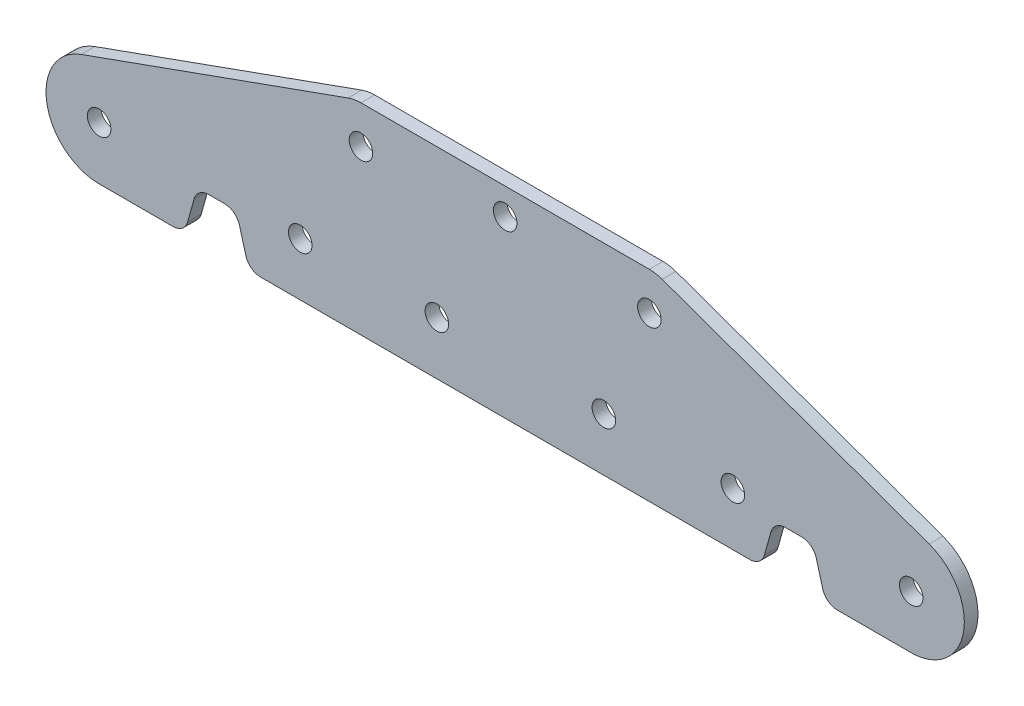
SolidWorks part; units mm, degrees
ref_plane "前视基准面" through (0, 0, 0) normal (0, 0, 1) x (1, 0, 0)
ref_plane "上视基准面" through (0, 0, 0) normal (0, 1, 0) x (1, 0, 0)
ref_plane "右视基准面" through (0, 0, 0) normal (1, 0, 0) x (0, 0, -1)
sketch "草图1" plane through (0, 0, 0) normal (0, 0, 1) x (1, 0, 0)
  line L0 (-60, 0) -> (60, 0) construction
  line L1 (-19, 10.5) -> (19, 10.5)
  line L2 (38, 15.2644) -> (38, -16) construction
  line L3 (-53.5, -16) -> (-42.25, -16)
  line L4 (33.75, -16) -> (35.4234, -10)
  line L5 (0, 9.057) -> (0, -9.6824) construction
  line L6 (-51.6434, 7) -> (46.247, 7) construction
  line L7 (-48.1899, -9) -> (48.1377, -9) construction
  line L8 (-40.25, 5.5) -> (37.7327, 5.5) construction
  line L9 (35.4234, -10) -> (40.5766, -10)
  line L10 (40.5766, -10) -> (42.25, -16)
  line L11 (42.25, -16) -> (53.5, -16)
  line L12 (-40.5766, -10) -> (-42.25, -16)
  line L13 (-33.75, -16) -> (-35.4234, -10)
  line L14 (-35.4234, -10) -> (-40.5766, -10)
  line L15 (-33.75, -16) -> (33.75, -16)
  line L16 (-20.6882, 10.2064) -> (-55.8635, -2.4111)
  line L17 (20.6882, 10.2064) -> (55.8635, -2.4111)
  circle A0 centre (-27, -9) radius 1.55
  circle A1 centre (-9, -9) radius 1.55
  arc A2 (-20.6882, 10.2064) -> (-19, 10.5) centre (-19, 5.5) cw
  circle A3 centre (13, -9) radius 1.55
  circle A4 centre (30, -9) radius 1.55
  circle A5 centre (0, 7) radius 1.55
  circle A6 centre (-53.5, -9) radius 1.55
  circle A7 centre (53.5, -9) radius 1.55
  circle A8 centre (-19, 5.5) radius 1.55
  circle A9 centre (19, 5.5) radius 1.55
  circle A10 centre (-19, 5.5) radius 3 construction
  arc A11 (-55.8635, -2.4111) -> (-53.5, -16) centre (-53.5, -9) ccw
  arc A12 (55.8635, -2.4111) -> (53.5, -16) centre (53.5, -9) cw
  arc A14 (20.6882, 10.2064) -> (19, 10.5) centre (19, 5.5) ccw
  point P0 (0, 0)
  dimension "D7" = 3.1
  dimension "D17" = 6
  dimension "D22" = 8.5
  dimension "D19" = 6
  dimension "D3" = 9
  dimension "D5" = 9
  dimension "D6" = 18
  dimension "D9" = 13
  dimension "D10" = 17
  dimension "D11" = 25
  dimension "D12" = 16
  dimension "D13" = 53.5
  dimension "D14" = 16
  dimension "D15" = 19
  dimension "D16" = 1.5
  dimension "D20" = 7
  dimension "D21" = 3.5
extrude "凸台-拉伸1" add sketch "草图1" along normal blind 1.8
fillet "圆角1" radius 2 8 edges at (-33.75, -16, 0.9) (-35.4234, -10, 0.9) (-42.25, -16, 0.9) (-40.5766, -10, 0.9) (42.25, -16, 0.9) (40.5766, -10, 0.9) (35.4234, -10, 0.9) (33.75, -16, 0.9)
